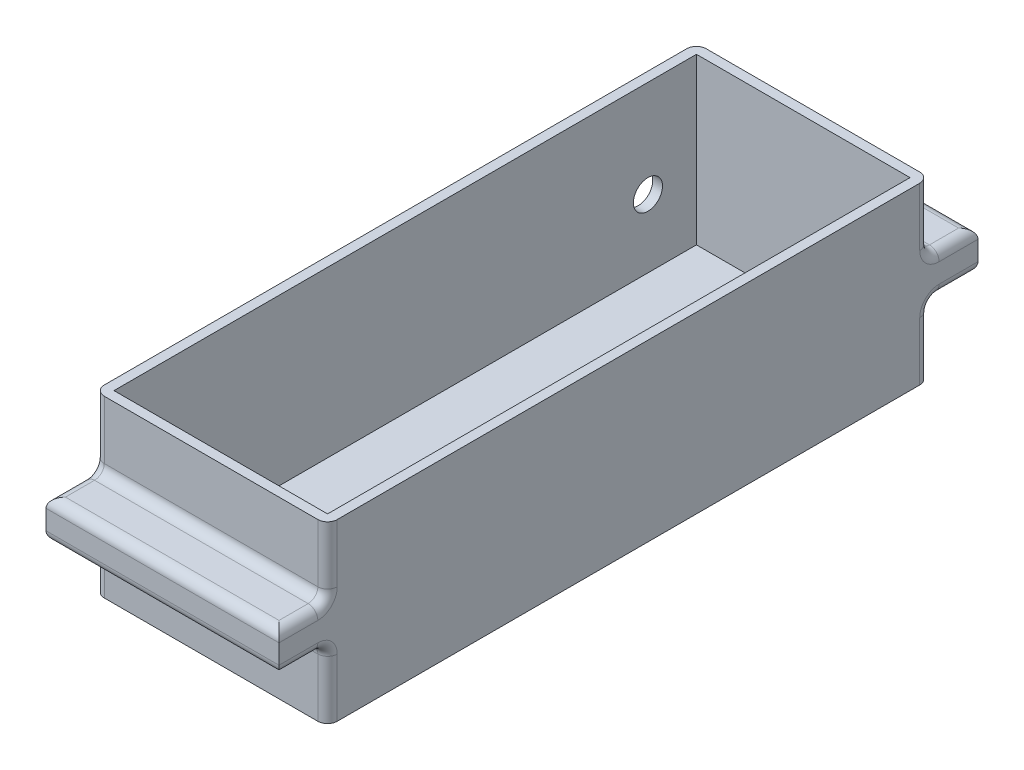
SolidWorks part; units mm, degrees
ref_plane "Front Plane" through (0, 0, 0) normal (0, 0, 1) x (1, 0, 0)
ref_plane "Top Plane" through (0, 0, 0) normal (0, 1, 0) x (1, 0, 0)
ref_plane "Right Plane" through (0, 0, 0) normal (1, 0, 0) x (0, 0, -1)
sketch "Sketch1" plane through (0, 0, 0) normal (0, 1, 0) x (1, 0, 0)
  line L0 (-300, 105) -> (-300, -105) construction
  line L1 (-250, 155) -> (300, 155) construction
  line L2 (-300, 105) -> (-300, -105)
  line L3 (-250, -155) -> (300, -155) construction
  line L4 (300, 155) -> (300, -155) construction
  line L5 (-250, 155) -> (-200, 155) construction
  line L6 (-250, -155) -> (-200, -155) construction
  line L7 (-200, 155) -> (-200, -155) construction
  line L8 (-250, 155) -> (-300, 105) construction
  line L9 (-250, -155) -> (-300, -105) construction
  line L10 (300, -155) -> (300, 155)
  line L11 (300, -155) -> (180, -155)
  line L12 (300, 155) -> (180, 155)
  line L13 (180, -155) -> (180, 155)
  point P0 (0, 0)
  dimension "D1" = 200
  dimension "D2" = 310
  dimension "D3" = 300
  dimension "D4" = 250
  dimension "D5" = 300
  dimension "D6" = 105
  dimension "D7" = 120
extrude "Boss-Extrude4" add sketch "Sketch1" along normal blind 90 contours L13 L11 L10 L12
shell "Shell2" thickness 5
sketch "Sketch2" plane through (180, 0, 0) normal (-1, 0, 0) x (0, 0, 1)
  line L0 (-155, 90) -> (-155, 0) construction
  line L1 (155, 0) -> (-155, 0) construction
  line L2 (0, -49.5) -> (0, 49.5) construction
  circle A0 centre (-125, 40) radius 7.4997
  circle A1 centre (125, 40) radius 7.4997
  dimension "D1" = 30
  dimension "D2" = 40
extrude "Cut-Extrude1" cut sketch "Sketch2" against normal blind 10
ref_plane "Plane1" through (0, 0, 180) normal (0, 0, 1) x (1, 0, 0)
sketch "Sketch3" plane through (0, 0, 180) normal (0, 0, 1) x (1, 0, 0)
  line L0 (300, 90) -> (300, 0) construction
  line L1 (180, 35) -> (300, 35)
  line L2 (180, 35) -> (180, 55)
  line L3 (180, 55) -> (300, 55)
  line L4 (300, 35) -> (300, 55)
  line L5 (180, 35) -> (300, 55) construction
  line L6 (180, 55) -> (300, 35) construction
  line L7 (300, 90) -> (180, 90) construction
  point P0 (240, 45)
  point P8 (300, 45)
  point P11 (240, 90)
  dimension "D1" = 20
extrude "Boss-Extrude5" add sketch "Sketch3" against normal up to next (25 mm away)
mirror "Mirror1" about plane through (0, 0, 0) normal (0, 0, 1) of "Boss-Extrude5"
sketch "Sketch4" plane through (180, 0, 0) normal (1, 0, 0) x (0, 0, -1)
  line L0 (-180, 35) -> (-180, 55) construction
  line L1 (-155, 35) -> (-155, 0) construction
  line L2 (180, 35) -> (180, 55) construction
  line L3 (155, 35) -> (155, 0) construction
  circle A0 centre (-170, 45) radius 2.5
  circle A1 centre (170, 45) radius 2.5
  point P5 (-180, 45)
  point P12 (180, 45)
  dimension "D1" = 15
  dimension "D2" = 15
extrude "Cut-Extrude2" cut sketch "Sketch4" along normal blind 20
fillet "Fillet1" radius 5 24 edges at (180, 72.5, -155) (300, 72.5, -155) (300, 72.5, 155) (180, 72.5, 155) (180, 35, -167.5) (300, 35, -167.5) (300, 55, -167.5) (180, 55, -167.5) (240, 55, -155) (300, 55, 167.5) (240, 55, 180) (180, 55, 167.5) (240, 55, 155) (180, 35, 167.5) (240, 35, 180) (300, 35, 167.5) (180, 17.5, 155) (240, 35, 155) (300, 17.5, 155) (240, 55, -180) (240, 35, -180) (300, 17.5, -155) (240, 35, -155) (180, 17.5, -155)
